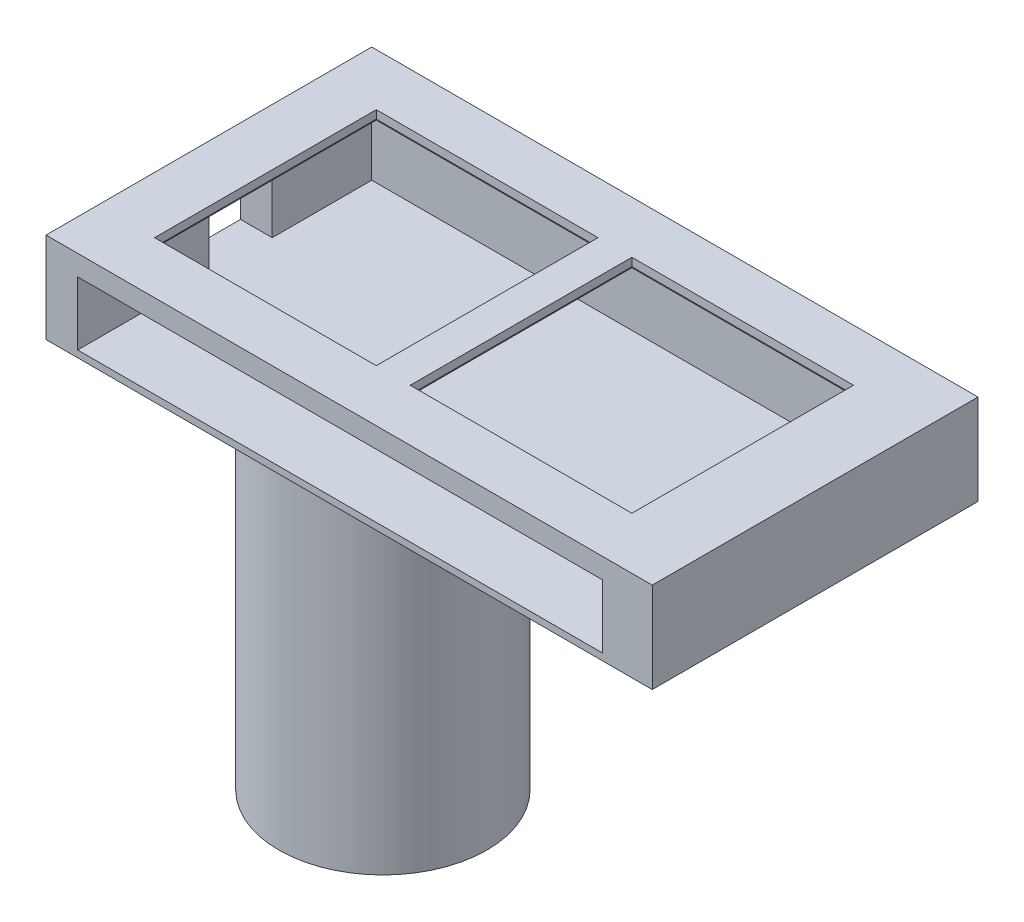
SolidWorks part; units mm, degrees
ref_plane "Front Plane" through (0, 0, 0) normal (0, 0, 1) x (1, 0, 0)
ref_plane "Top Plane" through (0, 0, 0) normal (0, 1, 0) x (1, 0, 0)
ref_plane "Right Plane" through (0, 0, 0) normal (1, 0, 0) x (0, 0, -1)
sketch "Sketch5" plane through (0, 0, 0) normal (0, 1, 0) x (1, 0, 0)
  line L0 (-124, 0) -> (-134, 0)
  line L1 (0, 0) -> (-1.9533, 0)
  line L2 (0, 0) -> (0, 72)
  line L3 (0, 72) -> (-134, 72)
  line L4 (-134, 0) -> (-134, 72)
  line L10 (-124, 0) -> (-1.9533, 0)
  dimension "D1" = 72
  dimension "D2" = 134
extrude "Main Body" add sketch "Sketch5" against normal blind 16
sketch "Sketch8" plane through (0, 0, 0) normal (0, 0, 1) x (1, 0, 0)
  line L0 (-134, -16) -> (-134, 0) construction
  line L1 (0, -16) -> (-134, -16)
  line L2 (0, -16) -> (0, -20)
  line L3 (0, -20) -> (-134, -20)
  line L4 (-134, -16) -> (-134, -20)
  dimension "D1" = 4
extrude "Cover" add sketch "Sketch8" against normal up to surface (72 mm away) up to face at (-67, -8, -72)
sketch "Sketch20" plane through (0, 0, 0) normal (0, 0, 1) x (1, 0, 0)
  line L0 (-134, -20) -> (-134, 0) construction
  line L1 (-11, -4.5) -> (-127, -4.5)
  line L2 (-11, -4.5) -> (-11, -18.5)
  line L3 (-11, -18.5) -> (-127, -18.5)
  line L4 (-127, -4.5) -> (-127, -18.5)
  line L6 (0, 0) -> (-134, 0) construction
  dimension "D1" = 7
  dimension "D2" = 116
  dimension "D3" = 14
  dimension "D4" = 4.5
extrude "Crystal Slot" cut sketch "Sketch20" against normal blind 65 contours L2 L1 L4 L3
sketch "Sketch9" plane through (-134, 0, 0) normal (-1, 0, 0) x (0, 0, 1)
  line L3 (-29, -4.5) -> (-43, -4.5)
  line L4 (-43, -18.5) -> (-43, -4.5)
  line L5 (-72, -20) -> (-72, 0) construction
  line L6 (-65, -4.5) -> (0, -4.5) construction
  line L7 (-29, -4.5) -> (-29, -18.5)
  line L8 (-29, -18.5) -> (-43, -18.5)
  dimension "D1" = 14
  dimension "D2" = 14
  dimension "D3" = 29
  dimension "D4" = 0
extrude "SiPM Window" cut sketch "Sketch9" against normal up to surface (7 mm away) up to face at (-127, -11.5, -32.5)
sketch "Sketch10" plane through (0, -20, 0) normal (0, -1, 0) x (1, 0, 0)
  line L1 (0, -36) -> (-72.5368, -36) construction
  line L2 (0, -72) -> (0, 0) construction
  line L3 (-134, -72) -> (-134, 0) construction
  line L6 (-95.5368, 0) -> (-95.5368, -13) construction
  line L7 (-134, 0) -> (0, 0) construction
  line L8 (-134, -72) -> (0, -72) construction
  line L9 (-95.5368, -59) -> (-95.5368, -72) construction
  line L10 (-118.5368, -36) -> (-134, -36) construction
  circle A0 centre (-95.5368, -36) radius 20
  circle A1 centre (-95.5368, -36) radius 23
  dimension "D2" = 46
  dimension "D1" = 40
extrude "Tube Adapter" add sketch "Sketch10" along normal blind 85
ref_plane "Plane1" through (-144, 0, 0) normal (-1, 0, 0) x (0, 0, 1)
sketch "Sketch21" plane through (0, -4.5, 0) normal (0, -1, 0) x (1, 0, 0)
  line L0 (-11, -65) -> (-11, 0) construction
  line L1 (-13.5, -9) -> (-67.5, -9)
  line L2 (-13.5, -9) -> (-13.5, -63)
  line L3 (-13.5, -63) -> (-67.5, -63)
  line L4 (-67.5, -9) -> (-67.5, -63)
  line L5 (-70, -9) -> (-124, -9)
  line L6 (-70, -9) -> (-70, -63)
  line L7 (-70, -63) -> (-124, -63)
  line L8 (-124, -9) -> (-124, -63)
  line L9 (-67.5, -36) -> (-13.5, -36) construction
  line L10 (0, -36) -> (-124, -36) construction
  line L11 (0, -72) -> (0, 0) construction
  line L13 (-124, -36) -> (-70, -36) construction
  dimension "D1" = 2.5
  dimension "D2" = 54
  dimension "D3" = 54
  dimension "D4" = 54
  dimension "D5" = 2.5
  dimension "D6" = 54
extrude "Filter Slot" cut sketch "Sketch21" against normal blind 2.7
sketch "Sketch24" plane through (0, -1.8, 0) normal (0, -1, 0) x (1, 0, 0)
  line L0 (-124, -9) -> (-124, -63) construction
  line L1 (-16, -11.5) -> (-65, -11.5)
  line L2 (-16, -11.5) -> (-16, -60.5)
  line L3 (-16, -60.5) -> (-65, -60.5)
  line L4 (-65, -11.5) -> (-65, -60.5)
  line L5 (-13.5, -9) -> (-67.5, -9) construction
  line L7 (-124, -63) -> (-70, -63) construction
  line L9 (-13.5, -63) -> (-13.5, -9) construction
  line L10 (-67.5, -63) -> (-13.5, -63) construction
  line L11 (-67.5, -9) -> (-67.5, -63) construction
  line L12 (-70, -9) -> (-124, -9) construction
  line L13 (-121.5, -11.5) -> (-72.5, -11.5)
  line L14 (-121.5, -11.5) -> (-121.5, -60.5)
  line L15 (-121.5, -60.5) -> (-72.5, -60.5)
  line L16 (-72.5, -11.5) -> (-72.5, -60.5)
  line L17 (-70, -63) -> (-70, -9) construction
  dimension "D1" = 2.5
  dimension "D2" = 2.5
  dimension "D3" = 2.5
  dimension "D4" = 2.5
  dimension "D5" = 2.5
  dimension "D6" = 2.5
  dimension "D7" = 2.5
  dimension "D8" = 2.5
extrude "Filter Window" cut sketch "Sketch24" against normal up to surface (1.8 mm away) up to face at (-67, 0, -36)
sketch "Sketch25" plane through (-144, 0, 0) normal (-1, 0, 0) x (0, 0, 1)
  line L0 (-36, -18.5) -> (-36, -105) construction
  line L1 (-23.5, -20) -> (-48.5, -20)
  line L2 (-23.5, -20) -> (-23.5, -29)
  line L3 (-23.5, -29) -> (-48.5, -29)
  line L4 (-48.5, -20) -> (-48.5, -29)
  line L5 (-43, -18.5) -> (-29, -18.5) construction
  line L6 (-59, -105) -> (-13, -105) construction
  line L7 (-13.5887, -20) -> (-62.0521, -20) construction
  line L8 (-72, -20) -> (0, -20) construction
  dimension "D1" = 25
  dimension "D2" = 12.5
  dimension "D3" = 9
extrude "Wire Slot" cut sketch "Sketch25" against normal up to surface (32.8507 mm away)
